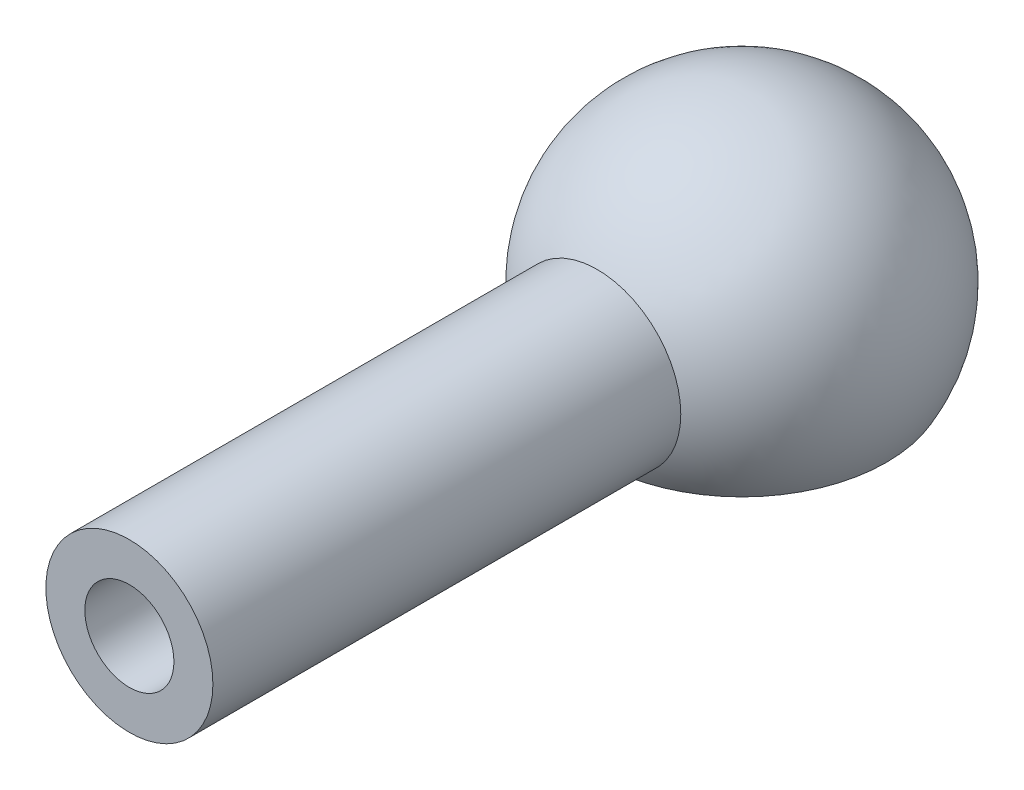
SolidWorks part; units mm, degrees
ref_plane "Front Plane" through (0, 0, 0) normal (0, 0, 1) x (1, 0, 0)
ref_plane "Top Plane" through (0, 0, 0) normal (0, 1, 0) x (1, 0, 0)
ref_plane "Right Plane" through (0, 0, 0) normal (1, 0, 0) x (0, 0, -1)
sketch "Sketch1" plane through (0, 0, 0) normal (0, 0, 1) x (1, 0, 0)
  line L0 (0, 0) -> (0, 3.75) construction
  line L1 (-3.2476, -1.875) -> (-2.1651, -1.25)
  line L2 (0, 2.5) -> (0, 3.75)
  arc A0 (0, 3.75) -> (-3.2476, -1.875) centre (0, 0) ccw
  arc A1 (-2.1651, -1.25) -> (0, 2.5) centre (0, 0) cw
  dimension "D1" = 2.5
  dimension "D3" = 120
  dimension "D2" = 1.25
revolve "Revolve1" add sketch "Sketch1" angle 360 about L2
ref_plane "Plane1" through (0, 0, 3.75) normal (0, 0, 1) x (1, 0, 0)
sketch "Sketch2" plane through (0, 0, 3.75) normal (0, 0, 1) x (1, 0, 0)
  line L0 (3.2476, -1.875) -> (-3.2476, -1.875) construction
  circle A0 centre (0, 0) radius 1.875
extrude "Boss-Extrude1" add sketch "Sketch2" along normal blind 10 and the other way up to next
sketch "Sketch5" plane through (0, 0, 13.75) normal (0, 0, 1) x (1, 0, 0)
  circle A0 centre (0, 0) radius 1
  dimension "D1" = 2
extrude "Cut-Extrude1" cut sketch "Sketch5" against normal blind 10
